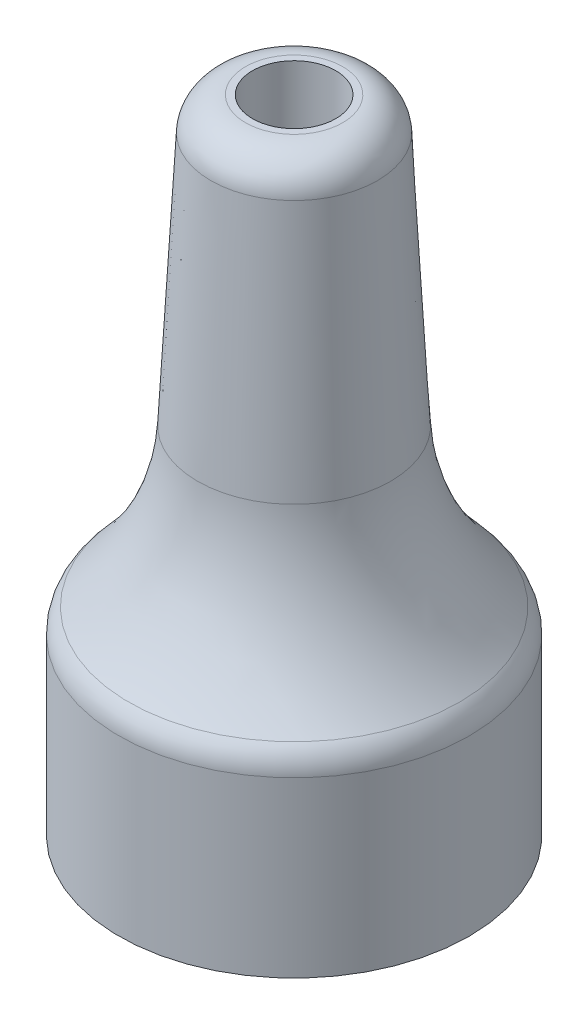
SolidWorks part; units mm, degrees
ref_plane "Front Plane" through (0, 0, 0) normal (0, 0, 1) x (1, 0, 0)
ref_plane "Top Plane" through (0, 0, 0) normal (0, 1, 0) x (1, 0, 0)
ref_plane "Right Plane" through (0, 0, 0) normal (1, 0, 0) x (0, 0, -1)
sketch "Sketch1" plane through (0, 0, 0) normal (0, 0, 1) x (1, 0, 0)
  line L0 (-2.35, 12.4829) -> (-3.0042, 0)
  line L1 (-3.0042, 0) -> (-5.05, 0)
  line L2 (-5.05, 0) -> (-5.05, -6)
  line L3 (-5.05, -6) -> (-3.95, -6)
  line L4 (-3.95, -6) -> (-3.95, -1)
  line L5 (-3.95, -1) -> (-1.2, -1)
  line L6 (-1.2, -1) -> (-1.2, 12.4829)
  line L7 (-1.2, 12.4829) -> (-2.35, 12.4829)
  line L8 (0, -1000) -> (0, 49000) construction
  dimension "D1" = 1.2
  dimension "D2" = 93
  dimension "D3" = 12.5
  dimension "D4" = 1
  dimension "D5" = 3.95
  dimension "D6" = 5.05
  dimension "D7" = 6
  dimension "D8" = 1.15
  dimension "D9" = 13.4829
revolve "Revolve1" add sketch "Sketch1" angle 360 about L8
fillet "Fillet1" radius 1 2 edges at (5.05, 0, 0) (2.35, 12.4829, 0)
fillet "Fillet2" radius 7 1 edges at (3.0042, 0, 0)
